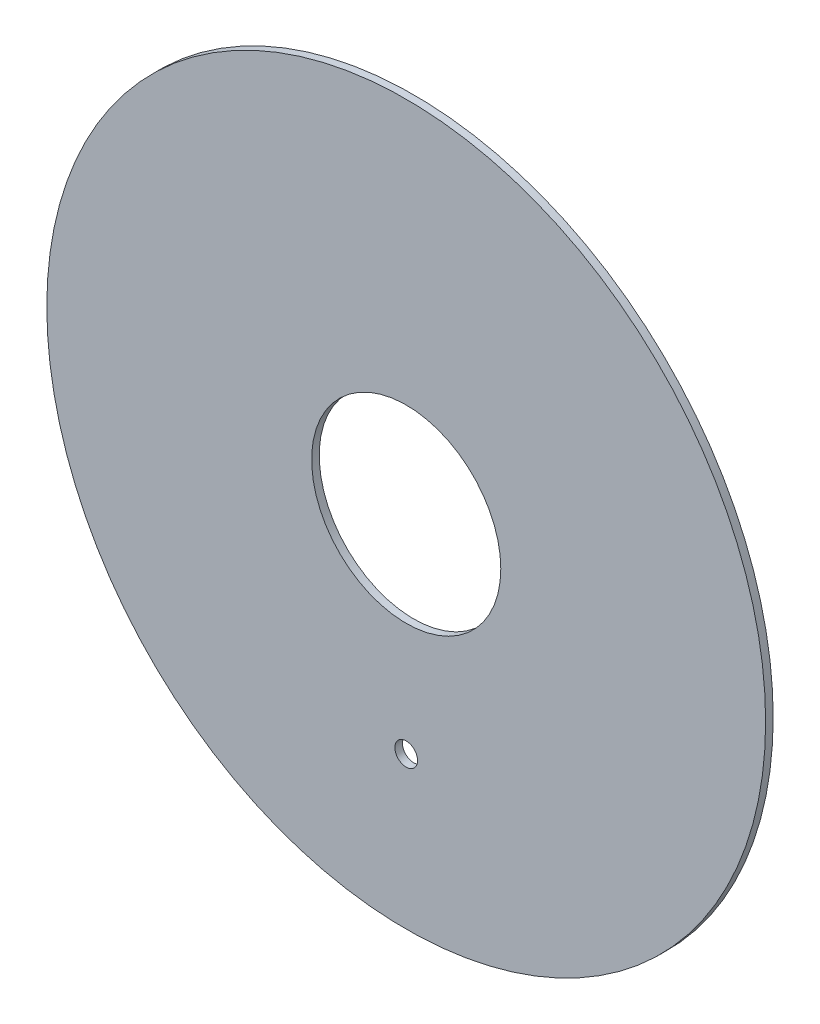
SolidWorks part; units mm, degrees
ref_plane "Plano frontal" through (0, 0, 0) normal (0, 0, 1) x (1, 0, 0)
ref_plane "Plano superior" through (0, 0, 0) normal (0, 1, 0) x (1, 0, 0)
ref_plane "Plano direito" through (0, 0, 0) normal (1, 0, 0) x (0, 0, -1)
sketch "Esboço1" plane through (0, 0, 0) normal (0, 0, 1) x (1, 0, 0)
  circle A0 centre (0, 0) radius 47.5
  circle A1 centre (0, 0) radius 12.5
extrude "Ressalto-extrusão1" add sketch "Esboço1" along normal blind 1
sketch "Esboço2" plane through (0, 0, 1) normal (0, 0, 1) x (1, 0, 0)
  circle A0 centre (0, -27.4538) radius 1.5
extrude "Corte-extrusão1" cut sketch "Esboço2" against normal blind 1
